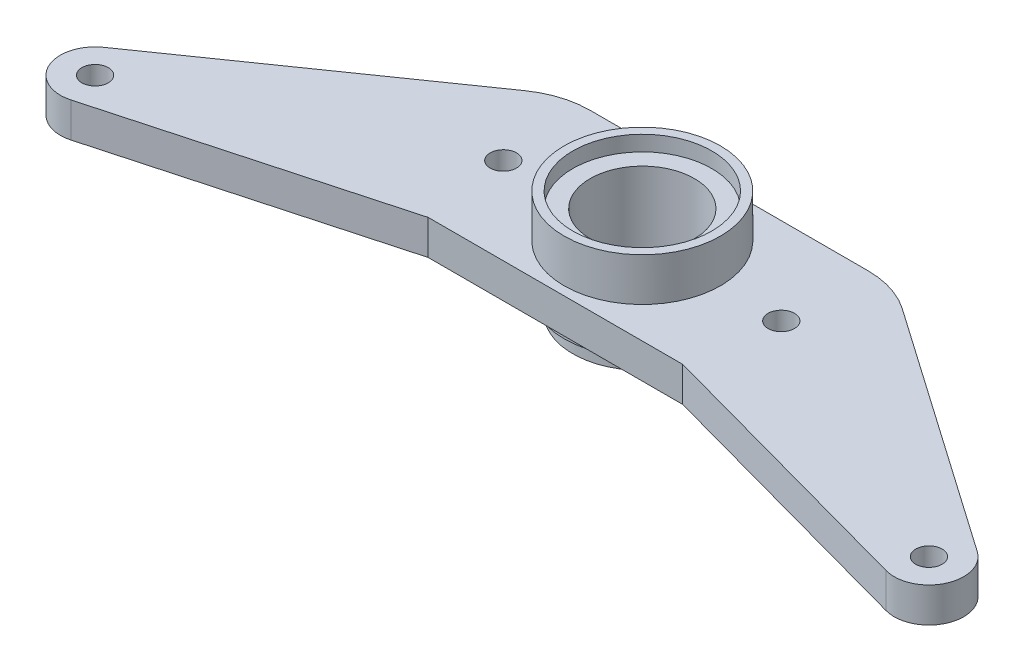
SolidWorks part; units mm, degrees
ref_plane "Front Plane" through (0, 0, 0) normal (0, 0, 1) x (1, 0, 0)
ref_plane "Top Plane" through (0, 0, 0) normal (0, 1, 0) x (1, 0, 0)
ref_plane "Right Plane" through (0, 0, 0) normal (1, 0, 0) x (0, 0, -1)
sketch "Sketch1" plane through (0, 0, 0) normal (0, 1, 0) x (1, 0, 0)
  line L0 (25.4, 0) -> (-25.4, 0) construction
  line L1 (25.4, -15.875) -> (-25.4, -15.875)
  line L2 (25.4, 15.875) -> (-25.4, 15.875)
  line L3 (-76.2, -23.8125) -> (-25.4, 0) construction
  line L4 (-79.8322, -18.6039) -> (-34.4804, 13.0216)
  line L5 (-74.5201, -29.9363) -> (-21.2003, -15.3094)
  line L6 (25.4, 0) -> (76.2, -23.8125) construction
  line L7 (34.4804, 13.0216) -> (79.8322, -18.6039)
  line L8 (21.2003, -15.3094) -> (74.5201, -29.9363)
  arc A0 (25.4, -15.875) -> (25.4, 15.875) centre (25.4, 0) ccw
  arc A1 (-25.4, 15.875) -> (-25.4, -15.875) centre (-25.4, 0) ccw
  arc A2 (-79.8322, -18.6039) -> (-74.5201, -29.9363) centre (-76.2, -23.8125) ccw
  arc A3 (-21.2003, -15.3094) -> (-34.4804, 13.0216) centre (-25.4, 0) ccw
  arc A4 (34.4804, 13.0216) -> (21.2003, -15.3094) centre (25.4, 0) ccw
  arc A5 (74.5201, -29.9363) -> (79.8322, -18.6039) centre (76.2, -23.8125) ccw
  point P2 (0, 0)
  point P10 (-50.8, -11.9063)
  point P15 (50.8, -11.9062)
  dimension "D5" = 6.35
  dimension "D1" = 31.75
  dimension "D2" = 50.8
  dimension "D3" = 23.8125
  dimension "D4" = 152.4
extrude "Boss-Extrude1" add sketch "Sketch1" along normal blind 6.35 contours L4 A2 L5 L1 A1 | L5 A3 A1 L1 | A4 L2 A3 L5 L1 L8 | A0 A4 L8 L1 | L8 A5 L7 A0 L1
sketch "Sketch2" plane through (0, 0, 0) normal (0, -1, 0) x (1, 0, 0)
  circle A0 centre (0, 0) radius 14.2875
  dimension "D1" = 28.575
extrude "Boss-Extrude2" add sketch "Sketch2" along normal blind 19.431 from offset 14.224 offset against normal yes
hole_wizard "Hole1" positions "Sketch3" profile "Sketch4" legacy
sketch "Sketch3" plane through (0, 14.224, 0) normal (0, 1, 0) x (1, 0, 0)
  point P0 (0, 0)
sketch "Sketch4" plane through (0, 14.224, 0) normal (1, 0, 0) x (0, 0, 1)
  line L0 (0, 0) -> (0, 19.05)
  line L1 (0, 19.05) -> (9.525, 19.05)
  line L2 (9.525, 19.05) -> (9.525, 2.794)
  line L3 (9.525, 2.794) -> (12.7, 2.794)
  line L4 (12.7, 2.794) -> (12.7, 0)
  line L5 (12.7, 0) -> (0, 0)
  line L6 (0, 110) -> (0, -10) construction
  dimension "Diameter" = 19.05
  dimension "Depth" = 19.05
  dimension "C-Bore Diameter" = 25.4
  dimension "C-Bore Depth" = 2.794
hole_wizard "#10-32 Tapped Hole1" positions "Sketch5" profile "Sketch6" tap size "#10-32" standard "ANSI Inch" end condition through all
sketch "Sketch5" plane through (0, 6.35, 0) normal (0, 1, 0) x (1, 0, 0)
  line L0 (-25.4, 0) -> (25.4, 0)
  point P0 (-25.4, 0)
  point P3 (25.4, 0)
  point P23 (-76.2, -23.8125)
  point P26 (76.2, -23.8125)
  dimension "D1" = 50.8
sketch "Sketch6" plane through (-25.4, 6.35, 0) normal (1, 0, 0) x (0, 0, 1)
  line L0 (0, 0) -> (0, 11.557)
  line L1 (0, 11.557) -> (2.413, 11.557)
  line L2 (2.413, 11.557) -> (2.413, 0)
  line L5 (2.413, 0) -> (0, 0)
  line L11 (0, -6.35) -> (0, 107.95) construction
  dimension "Thread Major Dia." = 4.826
  dimension "Thru Tap Drill Depth" = 11.557
sketch "Sketch7" plane through (0, -5.207, 0) normal (0, -1, 0) x (1, 0, 0)
  circle A0 centre (0, 0) radius 12.7
  circle A1 centre (0, 0) radius 14.2875 construction
  circle A2 centre (0, 0) radius 14.2875
  dimension "D2" = 1.5875
extrude "Cut-Extrude1" cut sketch "Sketch7" against normal blind 3.175
sketch "Sketch8" plane through (0, -5.207, 0) normal (0, -1, 0) x (1, 0, 0)
  line L1 (-9.5729, -4.5) -> (9.5729, -4.5)
  line L2 (-9.5729, -4.5) -> (-9.5729, 4.5)
  line L3 (-9.5729, 4.5) -> (9.5729, 4.5)
  line L4 (9.5729, -4.5) -> (9.5729, 4.5)
  line L5 (-9.5729, -4.5) -> (9.5729, 4.5) construction
  line L6 (-9.5729, 4.5) -> (9.5729, -4.5) construction
  point P0 (0, 0)
  dimension "D1" = 9
  dimension "D2" = 19.1459
